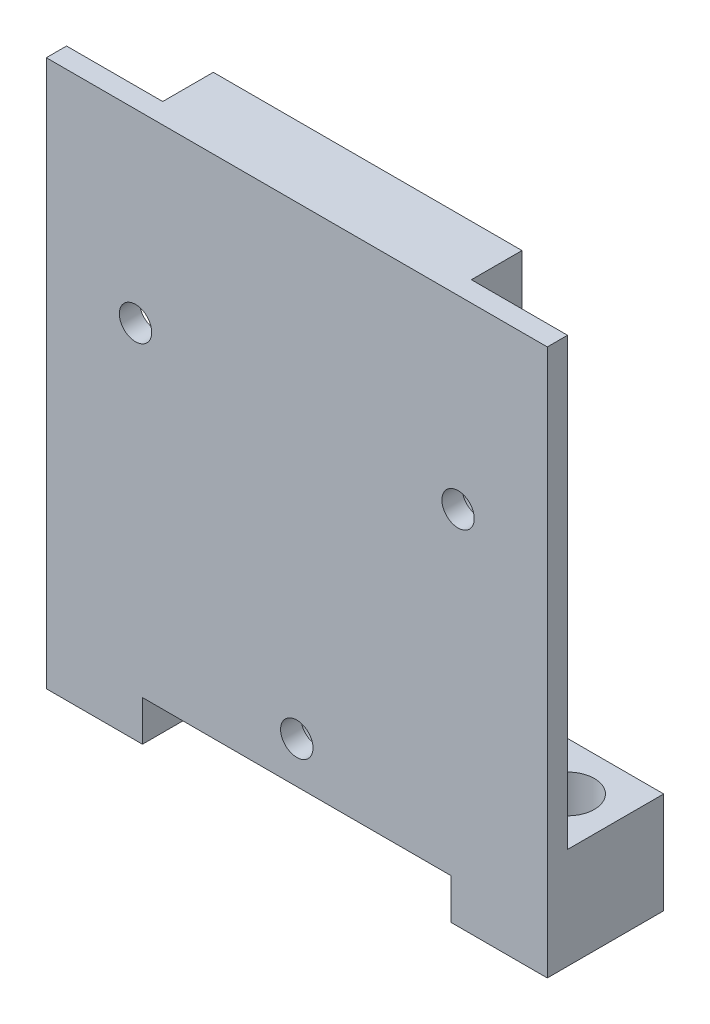
SolidWorks part; units mm, degrees
ref_plane "Front Plane" through (0, 0, 0) normal (0, 0, 1) x (1, 0, 0)
ref_plane "Top Plane" through (0, 0, 0) normal (0, 1, 0) x (1, 0, 0)
ref_plane "Right Plane" through (0, 0, 0) normal (1, 0, 0) x (0, 0, -1)
sketch "Sketch2" plane through (0, 0, 0) normal (0, 1, 0) x (1, 0, 0)
  line L0 (49.5, 4.75) -> (0, 4.75) construction
  line L5 (0, 9.5) -> (9.5, 9.5)
  line L6 (0, 9.5) -> (0, 0)
  line L7 (0, 0) -> (9.5, 0)
  line L8 (9.5, 9.5) -> (9.5, 0)
  line L9 (40, 9.5) -> (49.5, 9.5)
  line L10 (40, 9.5) -> (40, 0)
  line L11 (40, 0) -> (49.5, 0)
  line L12 (49.5, 9.5) -> (49.5, 0)
  line L13 (44.75, 9.5) -> (44.75, 0) construction
  line L14 (4.75, 9.5) -> (4.75, 0) construction
  circle A0 centre (4.75, 4.75) radius 2.65
  circle A1 centre (44.75, 4.75) radius 2.65
  point P0 (10.4606, 1.3099)
  dimension "D1" = 9.5
  dimension "D4" = 5.3
  dimension "D5" = 5.3
  dimension "D2" = 9.5
  dimension "D3" = 9.5
  dimension "D6" = 40
extrude "Boss-Extrude1" add sketch "Sketch2" along normal blind 10
sketch "Sketch13" plane through (0, 0, 0) normal (0, 0, 1) x (1, 0, 0)
  line L0 (49.5, 10) -> (49.5, 0) construction
  line L1 (0, 4) -> (49.5, 4)
  line L2 (0, 4) -> (0, 54)
  line L3 (0, 54) -> (49.5, 54)
  line L4 (49.5, 4) -> (49.5, 54)
  line L7 (0, 0) -> (9.5, 0) construction
  line L9 (0, 10) -> (0, 0) construction
  dimension "D2" = 50
  dimension "D1" = 4
extrude "Boss-Extrude4" add sketch "Sketch13" along normal blind 2
sketch "Sketch12" plane through (0, 0, 0) normal (0, 0, 1) x (1, 0, 0)
  line L0 (24.75, 49) -> (24.75, 4) construction
  line L1 (47.25, 26.5) -> (2.25, 26.5) construction
  line L2 (40, 4) -> (40, 0) construction
  line L3 (0, 0) -> (49.5, 0) construction
  line L4 (0, 4) -> (49.5, 4) construction
  line L5 (0, 4) -> (0, 0) construction
  line L6 (49.5, 4) -> (49.5, 0) construction
  line L7 (9.5, 4) -> (9.5, 0) construction
  line L11 (9.5, 4) -> (40, 4)
  circle A0 centre (24.75, 26.5) radius 22.5 construction
  circle A1 centre (24.75, 26.5) radius 18.4 construction
  circle A2 centre (24.75, 8.1) radius 1.6
  circle A3 centre (8.8151, 35.7) radius 1.6
  circle A4 centre (40.6849, 35.7) radius 1.6
  circle A5 centre (24.75, 8.1) radius 3
  circle A6 centre (8.8151, 35.7) radius 3
  circle A7 centre (40.6849, 35.7) radius 3
  point P19 (24.75, 26.5)
  point P31 (24.75, 26.5)
  point P40 (24.75, 26.5)
  dimension "D1" = 45
  dimension "D2" = 36.8
  dimension "D3" = 3.2
  dimension "D5" = 3
  dimension "D4" = 4
  dimension "D6" = 6
  dimension "D7" = 3
extrude "Cut-Extrude3" cut sketch "Sketch12" against normal blind 2 from surface at 2 contours A4 | A2 | A3 starting at face at (24.75, 29, 2)
sketch "Sketch14" plane through (0, 0, 0) normal (0, 0, -1) x (-1, 0, 0)
  line L0 (-9.5, 4) -> (-40, 4) construction
  line L1 (-40, 54) -> (-9.5, 54)
  line L2 (-40, 54) -> (-40, 4)
  line L3 (-40, 4) -> (-9.5, 4)
  line L4 (-9.5, 54) -> (-9.5, 4)
  line L5 (-9.5, 10) -> (-9.5, 4) construction
  line L6 (-49.5, 54) -> (0, 54) construction
  line L7 (-40, 4) -> (-40, 0) construction
  circle A0 centre (-40.6849, 35.7) radius 3
  circle A1 centre (-8.8151, 35.7) radius 3
  circle A2 centre (-24.75, 8.1) radius 3
  line M7 (-40, 10) -> (-40, 4)
  line M8 (-40, 4) -> (-9.5, 4)
  line M9 (-9.5, 4) -> (-9.5, 10)
  line M12 (0, 54) -> (-49.5, 54)
  dimension "D1" = 6
  dimension "D2" = 6
  dimension "D3" = 6
extrude "Boss-Extrude5" add sketch "Sketch14" along normal blind 5 contours A1 L4 L2 A0 A2 M12 M7 M8 M9
sketch "Sketch15" plane through (0, 0, 0) normal (0, 0, 1) x (1, 0, 0)
  line L1 (0, 4) -> (9.5, 4)
  line L2 (0, 4) -> (0, 0)
  line L3 (0, 0) -> (9.5, 0)
  line L4 (9.5, 4) -> (9.5, 0)
  line L5 (40, 4) -> (49.5, 4)
  line L6 (40, 4) -> (40, 0)
  line L7 (40, 0) -> (49.5, 0)
  line L8 (49.5, 4) -> (49.5, 0)
  point P10 (49.5, 0)
extrude "Boss-Extrude6" add sketch "Sketch15" along normal up to surface (2 mm away) up to face at (23.15, 8.1, 2)
